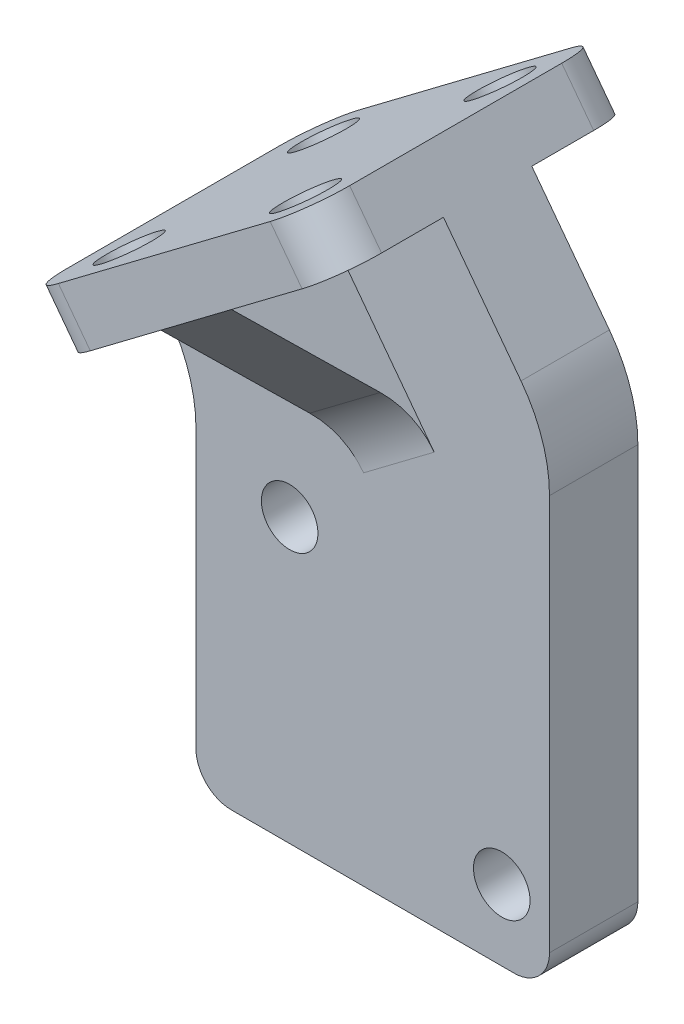
SolidWorks part; units mm, degrees
material "6061-T6 (SS)"
ref_plane "前视基准面" through (0, 0, 0) normal (0, 0, 1) x (1, 0, 0)
ref_plane "上视基准面" through (0, 0, 0) normal (0, 1, 0) x (1, 0, 0)
ref_plane "右视基准面" through (0, 0, 0) normal (1, 0, 0) x (0, 0, -1)
sketch "草图1" plane through (0, 0, 0) normal (0, 0, 1) x (1, 0, 0)
  line L0 (0, 2) -> (0, 17.7054)
  line L1 (-1.6109, 22.5199) -> (-1.9727, 23)
  line L2 (-1.9727, 23) -> (14, 35.0363)
  line L3 (14, 35.0363) -> (18.3891, 29.2118)
  line L4 (20, 24.3973) -> (20, 2)
  line L5 (18, 0) -> (2, 0)
  circle A0 centre (5.3, 16) radius 1.6
  circle A1 centre (17.3, 4) radius 1.6
  arc A2 (20, 2) -> (18, 0) centre (18, 2) cw
  arc A3 (0, 2) -> (2, 0) centre (2, 2) ccw
  arc A4 (18.3891, 29.2118) -> (20, 24.3973) centre (12, 24.3973) cw
  arc A5 (0, 17.7054) -> (-1.6109, 22.5199) centre (-8, 17.7054) ccw
  point P15 (20, 0)
  point P18 (0, 0)
  dimension "D2" = 12
  dimension "D3" = 12
  dimension "D4" = 5.3
  dimension "D5" = 4
  dimension "D6" = 3.2
  dimension "D11" = 2
  dimension "D12" = 8
  dimension "D1" = 20
  dimension "D7" = 37
  dimension "D8" = 20
  dimension "D9" = 23
  dimension "D10" = 6
extrude "凸台-拉伸1" add sketch "草图1" along normal blind 5
sketch "草图2" plane through (-11.769, 15.618, 0) normal (-0.6018, 0.7986, 0) x (0.7986, 0.6018, 0)
  line L0 (22.2663, 0) -> (22.2663, -2.5) construction
  line L1 (29.7663, -11) -> (14.7663, -11)
  line L2 (32.2663, -8.5) -> (32.2663, 3.5)
  line L3 (29.7663, 6) -> (14.7663, 6)
  line L4 (12.2663, -8.5) -> (12.2663, 3.5)
  line L5 (32.2663, -11) -> (12.2663, 6) construction
  line L6 (32.2663, 6) -> (12.2663, -11) construction
  line L7 (32.2663, 0) -> (12.2663, 0) construction
  line L8 (22.2663, -2.5) -> (12.2663, -2.5) construction
  line L9 (12.2663, -5) -> (12.2663, 0) construction
  line L10 (32.2663, -5) -> (32.2663, 0) construction
  line L12 (28.5163, -8) -> (16.0163, -8) construction
  line L13 (28.5163, -8) -> (28.5163, 3) construction
  line L14 (28.5163, 3) -> (16.0163, 3) construction
  line L15 (16.0163, -8) -> (16.0163, 3) construction
  line L16 (28.5163, -8) -> (16.0163, 3) construction
  line L17 (28.5163, 3) -> (16.0163, -8) construction
  arc A0 (14.7663, -11) -> (12.2663, -8.5) centre (14.7663, -8.5) cw
  arc A1 (32.2663, 3.5) -> (29.7663, 6) centre (29.7663, 3.5) ccw
  arc A2 (29.7663, -11) -> (32.2663, -8.5) centre (29.7663, -8.5) ccw
  arc A3 (14.7663, 6) -> (12.2663, 3.5) centre (14.7663, 3.5) ccw
  circle A4 centre (16.0163, 3) radius 1.6
  circle A5 centre (28.5163, 3) radius 1.6
  circle A6 centre (28.5163, -8) radius 1.6
  circle A7 centre (16.0163, -8) radius 1.6
  point P0 (22.2663, -2.5)
  dimension "D2" = 2.5
  dimension "D5" = 3.2
  dimension "D1" = 17
  dimension "D3" = 12.5
  dimension "D4" = 11
extrude "凸台-拉伸2" add sketch "草图2" along normal blind 3
sketch "草图6" plane through (25.769, 19.4183, 0) normal (0.7986, 0.6018, 0) x (0, 0, -1)
  line L0 (-11, 19.5558) -> (-5, 12.2627)
  line L1 (0, 12.2627) -> (6, 19.5558)
  line L2 (6, 19.5558) -> (0, 19.5558)
  line L3 (0, 19.5558) -> (0, 12.2627)
  line L4 (-5, 19.5558) -> (-11, 19.5558)
  line L5 (-5, 19.5558) -> (-5, 12.2627)
extrude "凸台-拉伸4" add sketch "草图6" against normal blind 5 from offset 7.5 offset against normal yes
fillet "圆角1" radius 5 2 edges at (10.4027, 23.1936, 0) (10.4027, 23.1936, 5)
